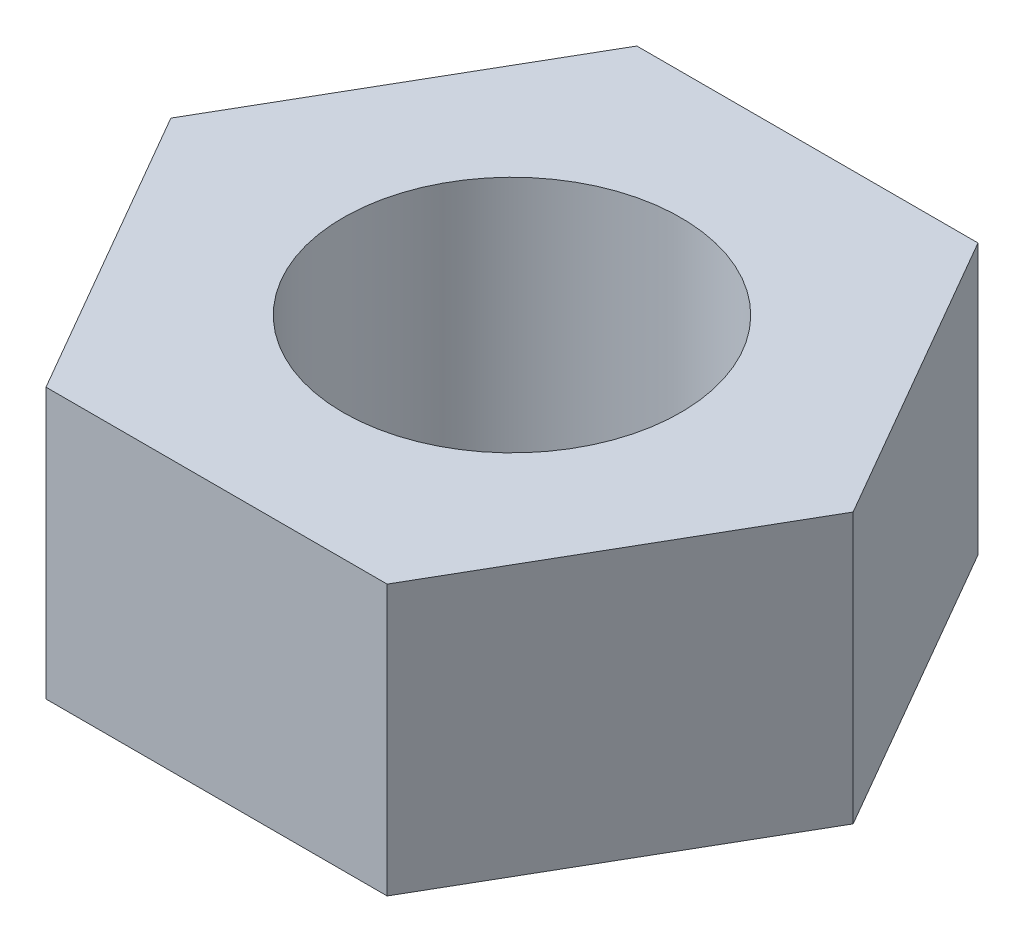
SolidWorks part; units mm, degrees
material "acero"
ref_plane "Alzado" through (0, 0, 0) normal (0, 0, 1) x (1, 0, 0)
ref_plane "Planta" through (0, 0, 0) normal (0, 1, 0) x (1, 0, 0)
ref_plane "Vista lateral" through (0, 0, 0) normal (1, 0, 0) x (0, 0, -1)
sketch "Croquis1" plane through (0, 0, 0) normal (0, 1, 0) x (1, 0, 0)
  line L1 (-2.0207, 3.5) -> (-4.0415, 0)
  line L2 (-4.0415, 0) -> (-2.0207, -3.5)
  line L3 (-2.0207, -3.5) -> (2.0207, -3.5)
  line L4 (2.0207, -3.5) -> (4.0415, 0)
  line L5 (4.0415, 0) -> (2.0207, 3.5)
  line L6 (2.0207, 3.5) -> (-2.0207, 3.5)
  circle A0 centre (0, 0) radius 3.5 construction
  circle A1 centre (0, 0) radius 2
  dimension "D1" = 4
  dimension "D2" = 7
extrude "Saliente-Extruir1" add sketch "Croquis1" along normal blind 3.2
